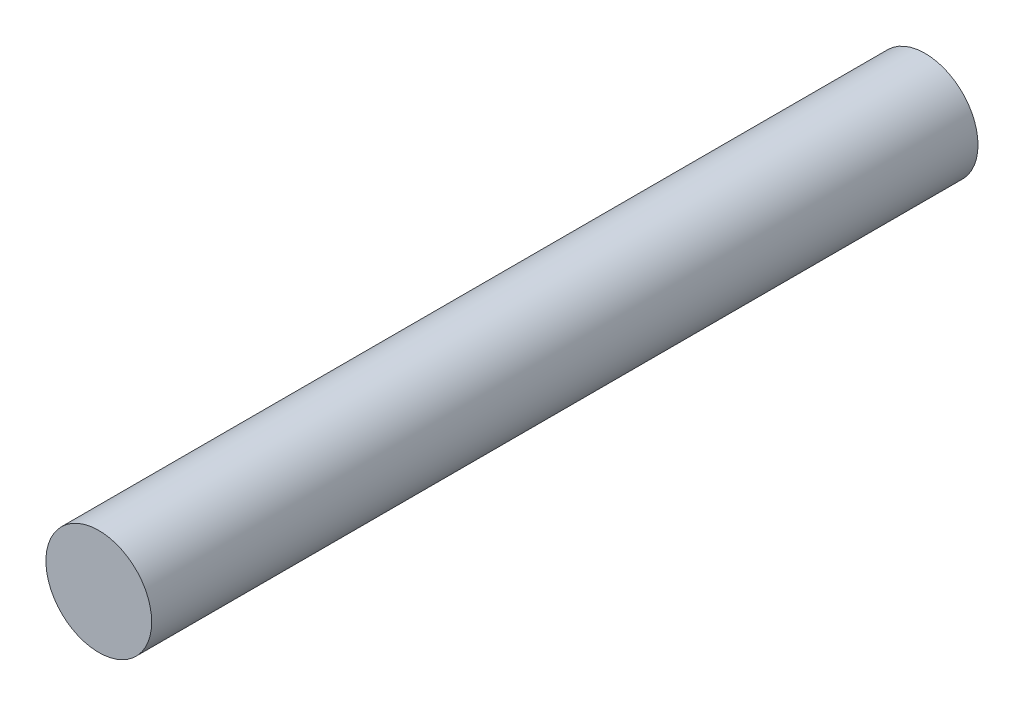
SolidWorks part; units mm, degrees
ref_plane "Front Plane" through (0, 0, 0) normal (0, 0, 1) x (1, 0, 0)
ref_plane "Top Plane" through (0, 0, 0) normal (0, 1, 0) x (1, 0, 0)
ref_plane "Right Plane" through (0, 0, 0) normal (1, 0, 0) x (0, 0, -1)
sketch "Sketch1" plane through (0, 0, 0) normal (0, 0, 1) x (1, 0, 0)
  circle A0 centre (0, 0) radius 1.6
  dimension "D1" = 3.2
extrude "Boss-Extrude1" add sketch "Sketch1" along normal mid plane 25
